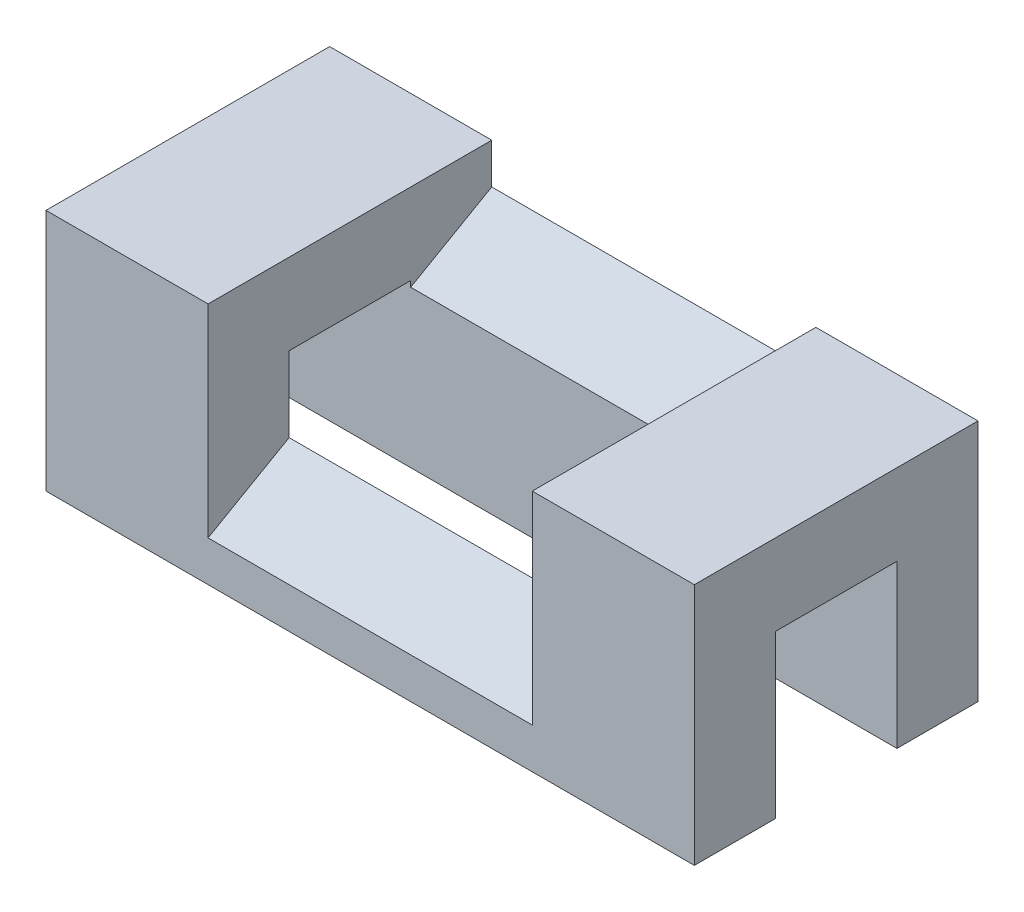
SolidWorks part; units mm, degrees
ref_plane "Front Plane" through (0, 0, 0) normal (0, 0, 1) x (1, 0, 0)
ref_plane "Top Plane" through (0, 0, 0) normal (0, 1, 0) x (1, 0, 0)
ref_plane "Right Plane" through (0, 0, 0) normal (1, 0, 0) x (0, 0, -1)
sketch "Sketch1" plane through (0, 0, 0) normal (1, 0, 0) x (0, 0, -1)
  line L0 (0, 0) -> (0, 30)
  line L1 (0, 30) -> (35, 30)
  line L2 (35, 30) -> (35, 0)
  line L3 (35, 0) -> (25, 0)
  line L4 (25, 0) -> (25, 20)
  line L5 (0, 0) -> (10, 0)
  line L6 (10, 0) -> (10, 20)
  line L7 (10, 20) -> (25, 20)
  dimension "D1" = 30
  dimension "D2" = 35
  dimension "D3" = 10
  dimension "D4" = 20
  dimension "D5" = 10
extrude "Boss-Extrude1" add sketch "Sketch1" along normal mid plane 80
sketch "Sketch2" plane through (0, 0, 0) normal (1, 0, 0) x (0, 0, -1)
  line L0 (35, 25) -> (0, 5)
  line L1 (35, 0) -> (35, 30) construction
  line L2 (0, 30) -> (0, 0) construction
  line L3 (0, 0) -> (10, 0) construction
  line L4 (0, 5) -> (0, 30)
  line L5 (0, 30) -> (35, 30)
  line L6 (35, 30) -> (35, 25)
  dimension "D1" = 5
  dimension "D2" = 5
extrude "Cut-Extrude2" cut sketch "Sketch2" against normal mid plane 40
